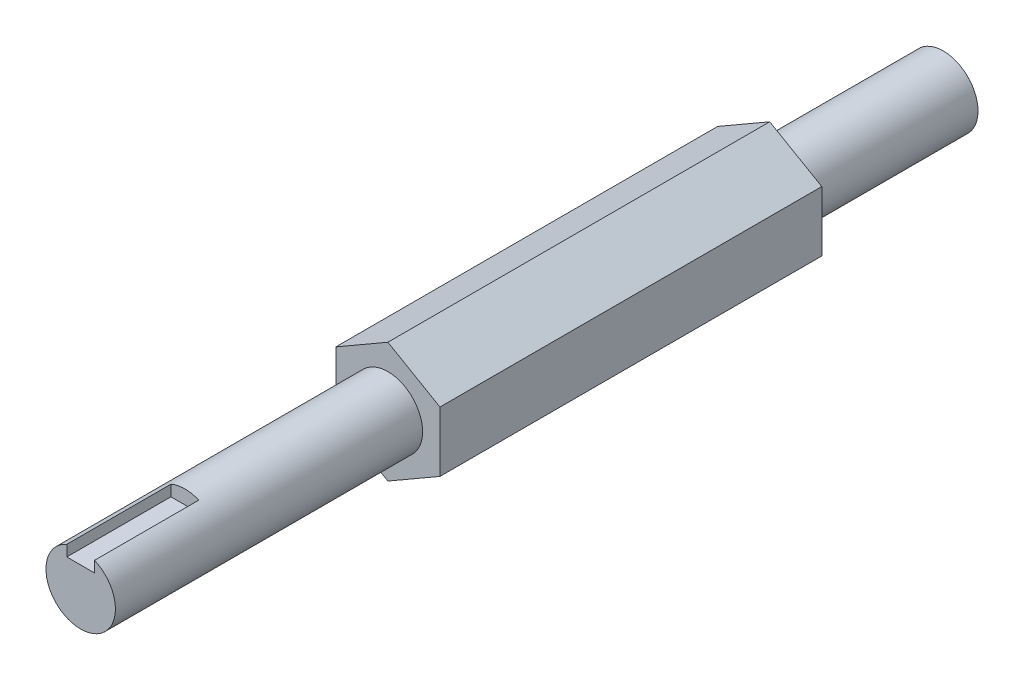
SolidWorks part; units mm, degrees
material "AISI 1045 Aço, trefilado"
ref_plane "Plano frontal" through (0, 0, 0) normal (0, 0, 1) x (1, 0, 0)
ref_plane "Plano superior" through (0, 0, 0) normal (0, 1, 0) x (1, 0, 0)
ref_plane "Plano direito" through (0, 0, 0) normal (1, 0, 0) x (0, 0, -1)
sketch "Esboço1" plane through (0, 0, 0) normal (0, 0, 1) x (1, 0, 0)
  line L1 (-15, 8.6603) -> (-15, -8.6603)
  line L2 (-15, -8.6603) -> (0, -17.3205)
  line L3 (0, -17.3205) -> (15, -8.6603)
  line L4 (15, -8.6603) -> (15, 8.6603)
  line L5 (15, 8.6603) -> (0, 17.3205)
  line L6 (0, 17.3205) -> (-15, 8.6603)
  circle A0 centre (0, 0) radius 15 construction
  dimension "D1" = 30
extrude "Ressalto-extrusão1" add sketch "Esboço1" along normal blind 110
sketch "Esboço2" plane through (0, 0, 110) normal (0, 0, 1) x (1, 0, 0)
  line L0 (15, -8.6603) -> (15, 8.6603) construction
  circle A0 centre (0, 0) radius 10
  dimension "D1" = 20
  dimension "D2" = 15
extrude "Ressalto-extrusão2" add sketch "Esboço2" along normal blind 88.5
sketch "Esboço3" plane through (0, 0, 0) normal (0, 0, -1) x (-1, 0, 0)
  circle A0 centre (0, 0) radius 10
  dimension "D1" = 20
extrude "Ressalto-extrusão3" add sketch "Esboço3" along normal blind 50
sketch "Esboço5" plane through (0, 0, 198.5) normal (0, 0, 1) x (1, 0, 0)
  line L1 (4, 6) -> (-4, 6)
  line L2 (4, 6) -> (4, 14)
  line L3 (4, 14) -> (-4, 14)
  line L4 (-4, 6) -> (-4, 14)
  line L5 (4, 6) -> (-4, 14) construction
  line L6 (4, 14) -> (-4, 6) construction
  line L7 (0, 10) -> (0, 0) construction
  circle A0 centre (0, 0) radius 10 construction
  point P0 (0, 10)
  dimension "D1" = 8
  dimension "D2" = 8
extrude "Corte-extrusão1" cut sketch "Esboço5" against normal blind 30
